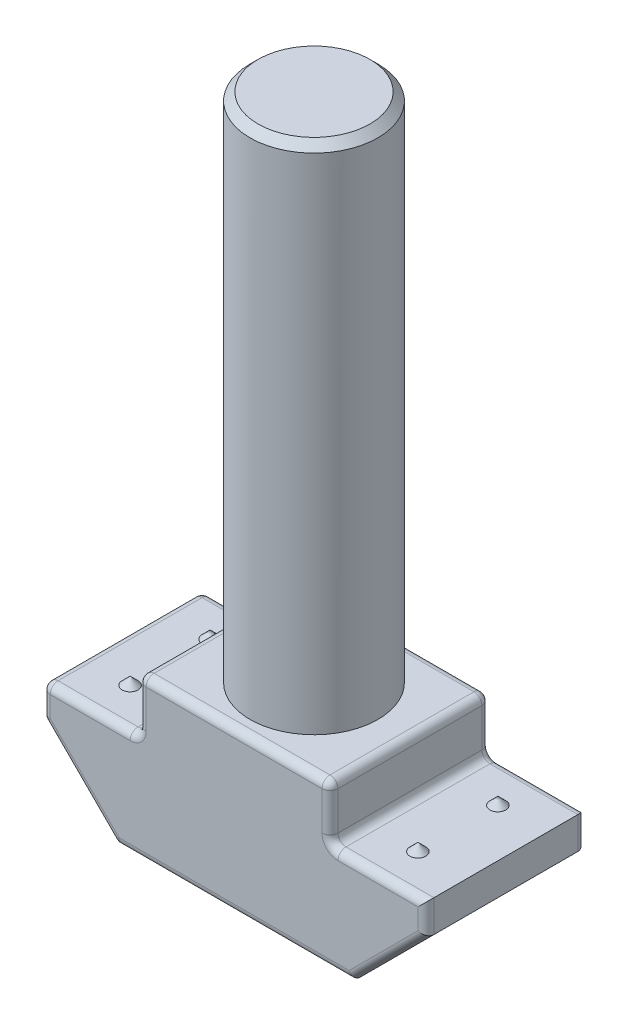
SolidWorks part; units mm, degrees
material "Acciaio inossidabile al cromo"
ref_plane "Piano frontale" through (0, 0, 0) normal (0, 0, 1) x (1, 0, 0)
ref_plane "Piano superiore" through (0, 0, 0) normal (0, 1, 0) x (1, 0, 0)
ref_plane "Piano destro" through (0, 0, 0) normal (1, 0, 0) x (0, 0, -1)
sketch "Schizzo1" plane through (0, 0, 0) normal (0, 0, 1) x (1, 0, 0)
  line L10 (3.7, 0) -> (-3.7, 0)
  line L11 (-3.7, 0) -> (-6, 2.3)
  line L12 (-6, 2.3) -> (-6, 3.3)
  line L13 (-6, 3.3) -> (-3, 3.3)
  line L14 (-3, 3.3) -> (-3, 5)
  line L15 (-3, 5) -> (3, 5)
  line L20 (0, 0) -> (0, 5) construction
  line L21 (0, -3.19) -> (0, 3.19) construction
  line L22 (6, 3.3) -> (3, 3.3)
  line L23 (6, 2.3) -> (6, 3.3)
  line L24 (3.7, 0) -> (6, 2.3)
  line L25 (3, 3.3) -> (3, 5)
  dimension "D1" = 3
  dimension "D2" = 3.3
  dimension "D3" = 1
  dimension "D4" = 45
  dimension "D5" = 6
  dimension "D6" = 5
extrude "Estrusione-Estrusione1" add sketch "Schizzo1" along normal blind 5
ref_plane "Piano1" through (0, 0, 2.5) normal (0, 0, 1) x (1, 0, 0)
fillet "Raccordo1" radius 0.25 27 edges at (3, 3.3, 2.5) (3, 5, 2.5) (-4.5, 3.3, 5) (0, 5, 5) (3, 4.15, 5) (4.5, 3.3, 5) (6, 2.8, 5) (4.85, 1.15, 5) (0, 0, 5) (-3, 5, 2.5) (-3, 4.15, 5) (-3, 3.3, 2.5) (-6, 3.3, 2.5) (-6, 2.8, 5) (-6, 2.3, 2.5) (-4.85, 1.15, 5) (-3.7, 0, 2.5) (0, 0, 0) (4.85, 1.15, 0) (6, 2.8, 0) (4.5, 3.3, 0) (3, 4.15, 0) (0, 5, 0) (-3, 4.15, 0) (-4.5, 3.3, 0) (-6, 2.8, 0) (-4.85, 1.15, 0)
sketch "Schizzo7" plane through (0, 5, 0) normal (0, 1, 0) x (1, 0, 0)
  line L0 (-2.75, -2.5) -> (2.75, -2.5) construction
  line L1 (-2.75, -0.25) -> (-2.75, -4.75) construction
  line L2 (2.75, -4.75) -> (2.75, -0.25) construction
  circle A0 centre (0, -2.5) radius 2
  dimension "D1" = 4
extrude "Estrusione-Estrusione3" add sketch "Schizzo7" along normal blind 16
cosmetic thread "Filettatura cosmetica1" parameters "D2"=3.22
chamfer "Smusso1" distance 0.25 angle 45 1 edges at (0, 21, 4.5)
ref_plane "Piano4" through (0, 0, 1.25) normal (0, 0, 1) x (1, 0, 0)
sketch "Schizzo8" plane through (0, 0, 1.25) normal (0, 0, 1) x (1, 0, 0)
  line L0 (-4.5, 3.3) -> (-4.5, 3.55)
  line L1 (-5.75, 3.3) -> (-3.25, 3.3) construction
  line L2 (-4.5, 3.55) -> (-4.75, 3.3)
  line L3 (-4.75, 3.3) -> (-4.5, 3.3)
  line L4 (-4.5, 3.3) -> (-4.5, 4.2152) construction
  dimension "D1" = 0.25
  dimension "D2" = 45
revolve "Rivoluzione2" add sketch "Schizzo8" angle 360 about L4
mirror "Specchia3" about plane through (0, 0, 0) normal (1, 0, 0) of "Rivoluzione2"
mirror "Specchia4" about plane through (0, 0, 2.5) normal (0, 0, 1) of "Specchia3", "Rivoluzione2"
